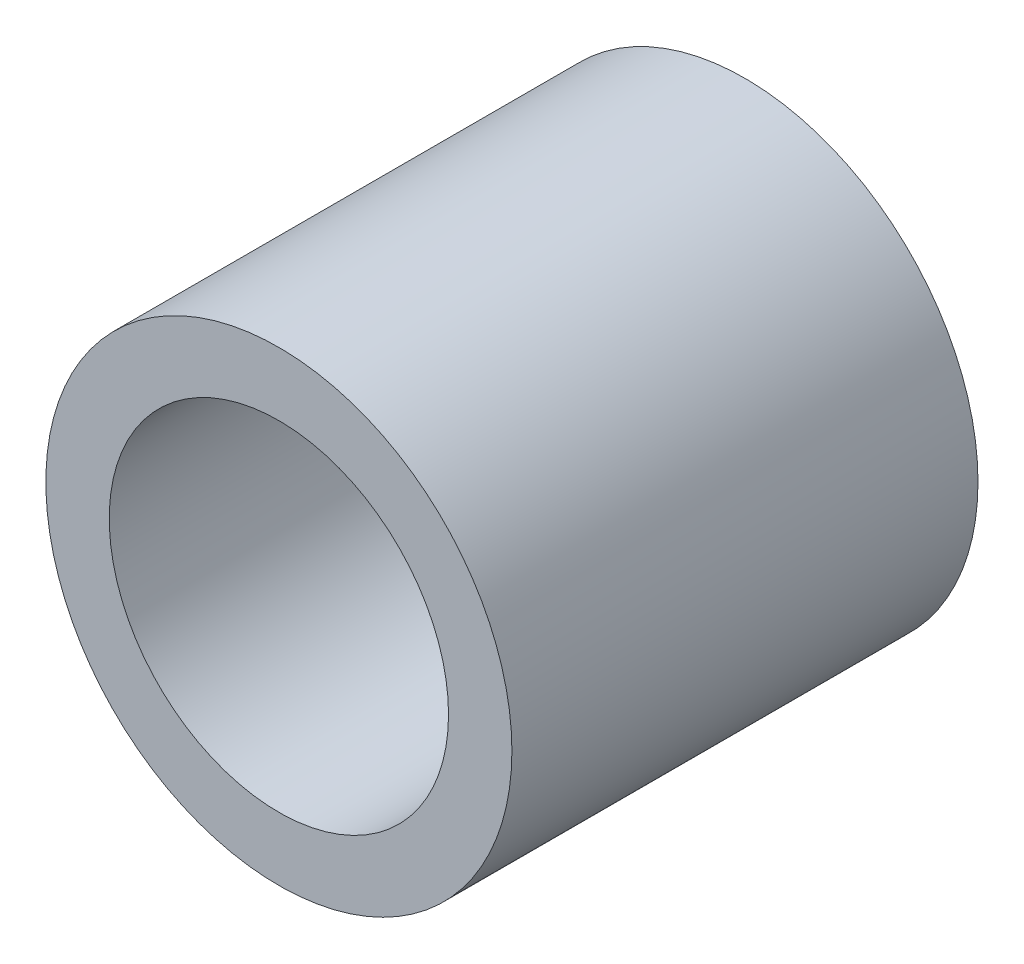
SolidWorks part; units mm, degrees
ref_plane "Front Plane" through (0, 0, 0) normal (0, 0, 1) x (1, 0, 0)
ref_plane "Top Plane" through (0, 0, 0) normal (0, 1, 0) x (1, 0, 0)
ref_plane "Right Plane" through (0, 0, 0) normal (1, 0, 0) x (0, 0, -1)
sketch "Sketch1" plane through (0, 0, 0) normal (0, 0, 1) x (1, 0, 0)
  circle A0 centre (0, 0) radius 12.5
extrude "Boss-Extrude1" add sketch "Sketch1" along normal blind 40
sketch "Sketch2" plane through (0, 0, 40) normal (0, 0, 1) x (1, 0, 0)
  circle A0 centre (0, 0) radius 19
extrude "Cut-Extrude1" cut sketch "Sketch2" against normal blind 15
sketch "Sketch3" plane through (0, 0, 0) normal (0, 0, -1) x (-1, 0, 0)
  line L1 (-2.6, 1.6) -> (2.6, 1.6)
  line L2 (-2.6, 1.6) -> (-2.6, -1.6)
  line L3 (-2.6, -1.6) -> (2.6, -1.6)
  line L4 (2.6, 1.6) -> (2.6, -1.6)
  dimension "D1" = 2.6
  dimension "D2" = 2.6
  dimension "D3" = 3.2
  dimension "D4" = 1.6
extrude "Cut-Extrude2" cut sketch "Sketch3" against normal blind 7
sketch "Sketch4" plane through (0, 0, 25) normal (0, 0, 1) x (1, 0, 0)
  circle A0 centre (0, 0) radius 9.1
extrude "Cut-Extrude3" cut sketch "Sketch4" against normal blind 15 contours A0
